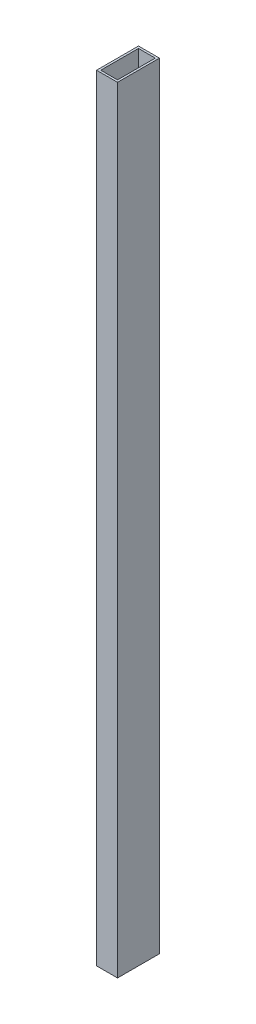
SolidWorks part; units mm, degrees
ref_plane "Спереди" through (0, 0, 0) normal (0, 0, 1) x (1, 0, 0)
ref_plane "Сверху" through (0, 0, 0) normal (0, 1, 0) x (1, 0, 0)
ref_plane "Справа" through (0, 0, 0) normal (1, 0, 0) x (0, 0, -1)
sketch "Эскиз1" plane through (0, 0, 0) normal (0, 1, 0) x (1, 0, 0)
  line L1 (-10, 20) -> (10, 20)
  line L2 (-10, 20) -> (-10, -20)
  line L3 (-10, -20) -> (10, -20)
  line L4 (10, 20) -> (10, -20)
  line L5 (-10, 20) -> (10, -20) construction
  line L6 (-10, -20) -> (10, 20) construction
  point P0 (0, 0)
extrude "Вытянуть-Тонкостенный1" add sketch "Эскиз1" along normal blind 740 thin
